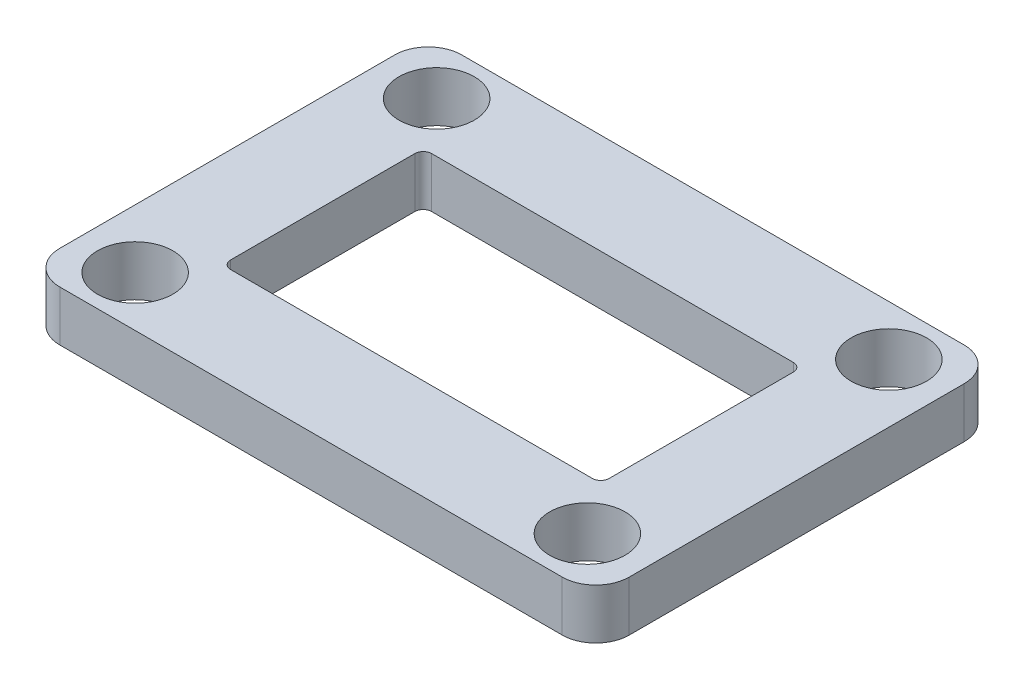
SolidWorks part; units mm, degrees
ref_plane "Front Plane" through (0, 0, 0) normal (0, 0, 1) x (1, 0, 0)
ref_plane "Top Plane" through (0, 0, 0) normal (0, 1, 0) x (1, 0, 0)
ref_plane "Right Plane" through (0, 0, 0) normal (1, 0, 0) x (0, 0, -1)
sketch "Sketch1" plane through (0, 0, 0) normal (0, 1, 0) x (1, 0, 0)
  line L1 (-11.3, -6) -> (11.3, -6)
  line L2 (-11.3, -6) -> (-11.3, 6)
  line L3 (-11.3, 6) -> (11.3, 6)
  line L4 (11.3, -6) -> (11.3, 6)
  line L5 (-11.3, -6) -> (11.3, 6) construction
  line L6 (-11.3, 6) -> (11.3, -6) construction
  line L7 (-17, -12) -> (17, -12)
  line L8 (-17, -12) -> (-17, 12)
  line L9 (-17, 12) -> (17, 12)
  line L10 (17, -12) -> (17, 12)
  line L11 (-17, -12) -> (17, 12) construction
  line L12 (-17, 12) -> (17, -12) construction
  line L24 (0, 0) -> (0, -8.1855) construction
  line L25 (0, 0) -> (4.9428, 0) construction
  circle A0 centre (-13.5, -9) radius 2.25
  circle A1 centre (-13.5, 9) radius 2.25
  circle A2 centre (13.5, -9) radius 2.25
  circle A3 centre (13.5, 9) radius 2.25
  point P0 (0, 0)
  point P6 (0, 0)
  dimension "D5" = 4.5
  dimension "D1" = 34
  dimension "D2" = 22.6
  dimension "D3" = 12
  dimension "D4" = 24
  dimension "D7" = 13.5
  dimension "D8" = 9
extrude "Boss-Extrude1" add sketch "Sketch1" along normal blind 3
fillet "Fillet1" radius 0.5 4 edges at (11.3, 1.5, 6) (11.3, 1.5, -6) (-11.3, 1.5, -6) (-11.3, 1.5, 6)
fillet "Fillet2" radius 2 4 edges at (17, 1.5, -12) (17, 1.5, 12) (-17, 1.5, 12) (-17, 1.5, -12)
sketch "Sketch2" plane through (0, 3, 0) normal (0, 1, 0) x (1, 0, 0)
  line L4 (11.3, -5.5) -> (11.3, 5.5)
  line L5 (-10.8, -6) -> (10.8, -6)
  line L6 (-11.3, 5.5) -> (-11.3, -5.5)
  line L7 (10.8, 6) -> (-10.8, 6)
  line L8 (11.3, -5.5) -> (11.3, 5.5)
  line L9 (-10.8, -6) -> (10.8, -6)
  line L10 (-11.3, 5.5) -> (-11.3, -5.5)
  line L11 (10.8, 6) -> (-10.8, 6)
  line L12 (17, -10) -> (17, 10)
  line L13 (15, 12) -> (-15, 12)
  line L14 (-17, 10) -> (-17, -10)
  line L15 (-15, -12) -> (15, -12)
  line L16 (17, -10) -> (17, 10)
  line L17 (15, 12) -> (-15, 12)
  line L18 (-17, 10) -> (-17, -10)
  line L19 (-15, -12) -> (15, -12)
  circle A1 centre (-13.5, -9) radius 2.25
  circle A2 centre (-13.5, -9) radius 2.25
  circle A3 centre (-13.5, 9) radius 2.25
  circle A4 centre (-13.5, 9) radius 2.25
  circle A5 centre (13.5, -9) radius 2.25
  arc A6 (10.8, -6) -> (11.3, -5.5) centre (10.8, -5.5) ccw
  arc A7 (-11.3, -5.5) -> (-10.8, -6) centre (-10.8, -5.5) ccw
  arc A8 (-10.8, 6) -> (-11.3, 5.5) centre (-10.8, 5.5) ccw
  arc A9 (11.3, 5.5) -> (10.8, 6) centre (10.8, 5.5) ccw
  arc A10 (10.8, -6) -> (11.3, -5.5) centre (10.8, -5.5) ccw
  arc A11 (-11.3, -5.5) -> (-10.8, -6) centre (-10.8, -5.5) ccw
  arc A12 (-10.8, 6) -> (-11.3, 5.5) centre (-10.8, 5.5) ccw
  arc A13 (11.3, 5.5) -> (10.8, 6) centre (10.8, 5.5) ccw
  circle A14 centre (13.5, -9) radius 2.25
  circle A15 centre (13.5, 9) radius 2.25
  circle A16 centre (13.5, 9) radius 2.25
  arc A20 (17, 10) -> (15, 12) centre (15, 10) ccw
  arc A21 (-15, 12) -> (-17, 10) centre (-15, 10) ccw
  arc A22 (-17, -10) -> (-15, -12) centre (-15, -10) ccw
  arc A23 (15, -12) -> (17, -10) centre (15, -10) ccw
  arc A24 (17, 10) -> (15, 12) centre (15, 10) ccw
  arc A25 (-15, 12) -> (-17, 10) centre (-15, 10) ccw
  arc A26 (-17, -10) -> (-15, -12) centre (-15, -10) ccw
  arc A27 (15, -12) -> (17, -10) centre (15, -10) ccw
  dimension "D1" = 0
  dimension "D2" = 0
  dimension "D3" = 0
  dimension "D4" = 0
  dimension "D5" = 0
  dimension "D6" = 0
